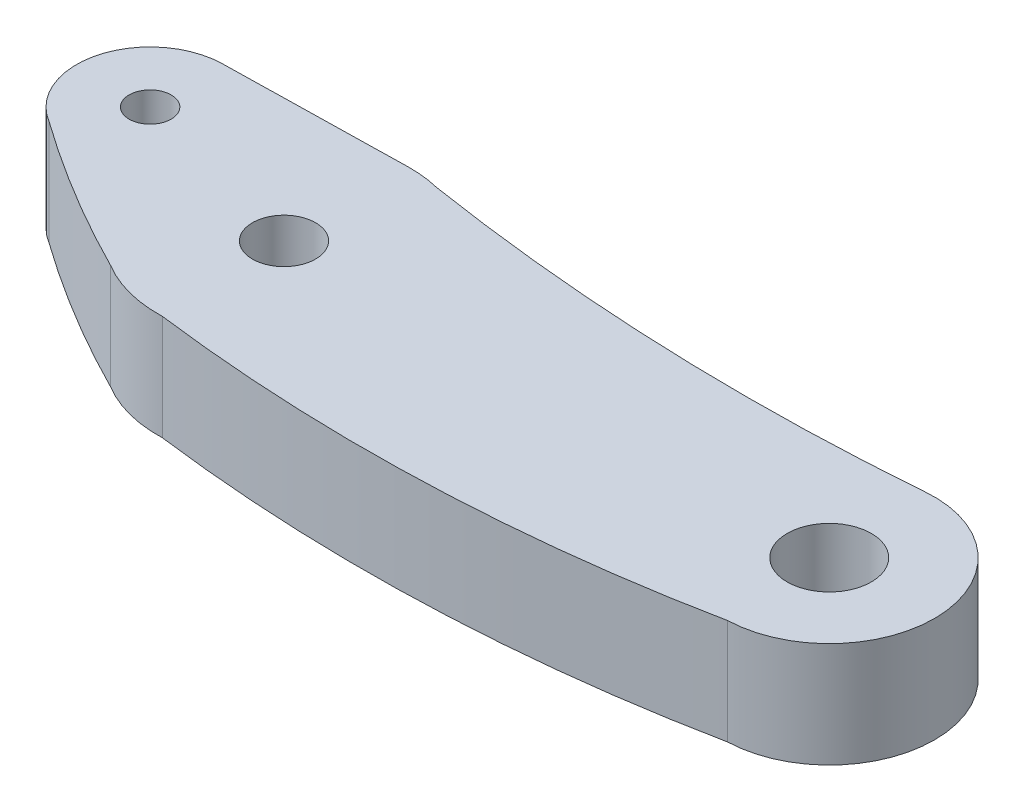
SolidWorks part; units mm, degrees
ref_plane "Front Plane" through (0, 0, 0) normal (0, 0, 1) x (1, 0, 0)
ref_plane "Top Plane" through (0, 0, 0) normal (0, 1, 0) x (1, 0, 0)
ref_plane "Right Plane" through (0, 0, 0) normal (1, 0, 0) x (0, 0, -1)
sketch "Sketch1" plane through (0, 0, 0) normal (0, 1, 0) x (1, 0, 0)
  line L0 (441.4866, 311.8757) -> (463.5413, 311.8757) construction
  line L1 (0, 0) -> (-1.5, 0)
  line L3 (0, 0) -> (-1.4489, 0.3882)
  line L4 (-8.7622, 5.8287) -> (-0.1181, 5.9988)
  line L7 (-7.7274, 2.0706) -> (-8.6933, 2.3294)
  circle A0 centre (0, 0) radius 1.5
  circle A1 centre (26, -0.0822) radius 2
  arc A2 (26.1756, -5.0851) -> (25.5399, 4.9026) centre (26, -0.0822) ccw
  circle A3 centre (-8.6933, 2.3294) radius 1
  arc A4 (1.4319, 5.8266) -> (-0.1181, 5.9988) centre (0, 0) ccw
  arc A5 (-8.7622, 5.8287) -> (-10.5026, -0.6667) centre (-8.6933, 2.3294) ccw
  arc A6 (0.2104, -5.9963) -> (26.1756, -5.0851) centre (10.4244, 73.349) ccw
  arc A7 (1.4319, 5.8266) -> (25.5399, 4.9026) centre (17.3652, 106.5745) ccw
  arc A8 (-10.5026, -0.6667) -> (-3.1017, -5.1361) centre (22.4029, 45.4597) ccw
  arc A10 (-5.3126, 1.4235) -> (-5.2431, 2.9173) centre (-8.6933, 2.3294) ccw
  arc A11 (-3.1017, -5.1361) -> (0.2104, -5.9963) centre (0, 0) ccw
  dimension "D1" = 3
  dimension "D3" = 12
  dimension "D5" = 7
  dimension "D7" = 5.006
  dimension "D2" = 26
  dimension "D4" = 9
  dimension "D6" = 15
extrude "Boss-Extrude1" add sketch "Sketch1" along normal blind 5
